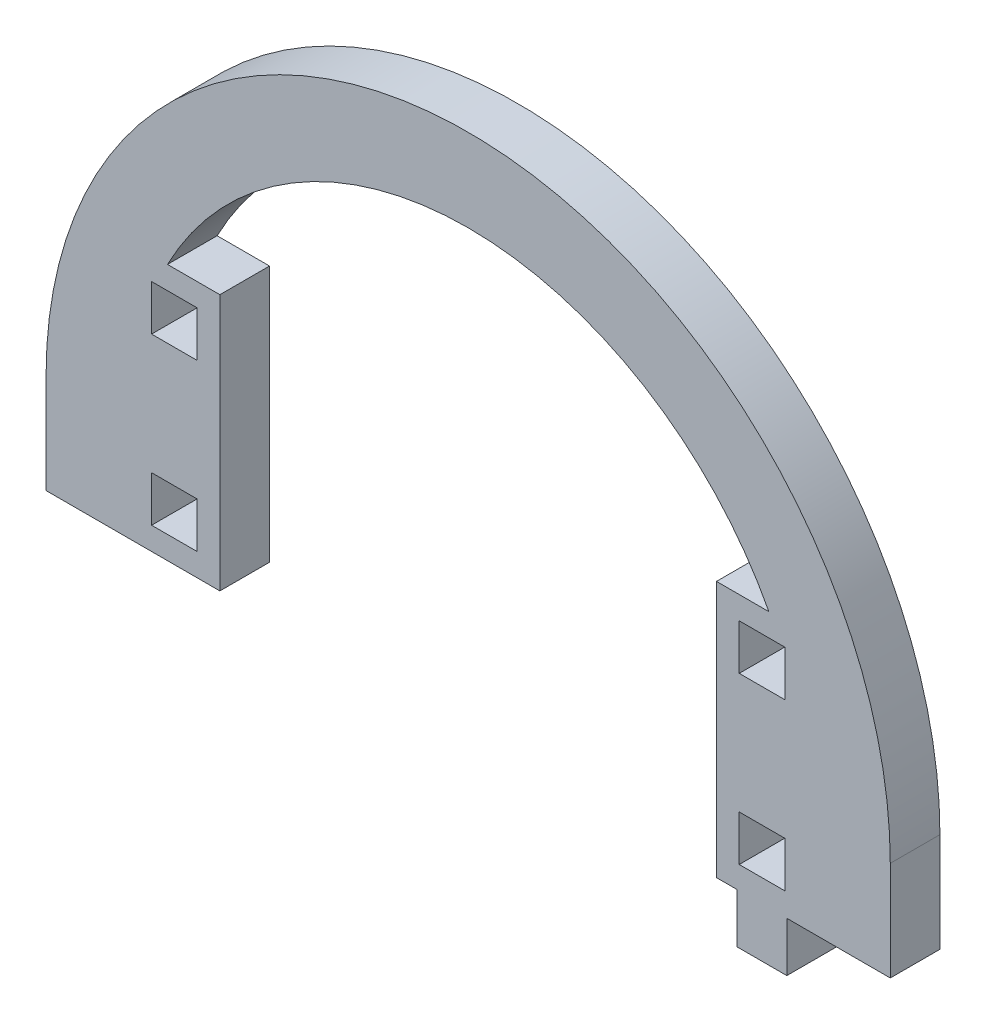
SolidWorks part; units mm, degrees
ref_plane "Front Plane" through (0, 0, 0) normal (0, 0, 1) x (1, 0, 0)
ref_plane "Top Plane" through (0, 0, 0) normal (0, 1, 0) x (1, 0, 0)
ref_plane "Right Plane" through (0, 0, 0) normal (1, 0, 0) x (0, 0, -1)
sketch "Model" plane through (0, 0, 0) normal (0, 0, 1) x (1, 0, 0)
  line L0 (3012.6171, 1236.9472) -> (3012.6171, 1224.9472)
  line L1 (3114.6171, 1236.9472) -> (3114.6171, 1224.9472)
  line L2 (3022.6171, 1224.9472) -> (3012.6171, 1224.9472)
  line L3 (3101.8671, 1233.1972) -> (3096.3671, 1233.1972)
  line L4 (3096.3671, 1233.1972) -> (3096.3671, 1227.6972)
  line L5 (3096.3671, 1227.6972) -> (3101.8671, 1227.6972)
  line L6 (3101.8671, 1227.6972) -> (3101.8671, 1233.1972)
  line L7 (3093.6171, 1224.9472) -> (3096.1171, 1224.9472)
  line L8 (3096.1171, 1224.9472) -> (3096.1171, 1218.9472)
  line L9 (3096.1171, 1218.9472) -> (3102.1171, 1218.9472)
  line L10 (3102.1171, 1218.9472) -> (3102.1171, 1224.9472)
  line L11 (3101.8671, 1253.1972) -> (3096.3671, 1253.1972)
  line L12 (3096.3671, 1253.1972) -> (3096.3671, 1247.6972)
  line L13 (3096.3671, 1247.6972) -> (3101.8671, 1247.6972)
  line L14 (3101.8671, 1247.6972) -> (3101.8671, 1253.1972)
  line L15 (3099.9489, 1255.9472) -> (3093.6171, 1255.9472)
  line L16 (3030.8671, 1233.1972) -> (3025.3671, 1233.1972)
  line L17 (3025.3671, 1233.1972) -> (3025.3671, 1227.6972)
  line L18 (3025.3671, 1227.6972) -> (3030.8671, 1227.6972)
  line L19 (3030.8671, 1227.6972) -> (3030.8671, 1233.1972)
  line L20 (3022.6171, 1224.9472) -> (3033.6171, 1224.9472)
  line L21 (3030.8671, 1253.1972) -> (3025.3671, 1253.1972)
  line L22 (3025.3671, 1253.1972) -> (3025.3671, 1247.6972)
  line L23 (3025.3671, 1247.6972) -> (3030.8671, 1247.6972)
  line L24 (3030.8671, 1247.6972) -> (3030.8671, 1253.1972)
  line L25 (3033.6171, 1255.9472) -> (3027.2853, 1255.9472)
  line L26 (3033.6171, 1255.9472) -> (3033.6171, 1224.9472)
  line L27 (3093.6171, 1255.9472) -> (3093.6171, 1224.9472)
  line L28 (3102.1171, 1224.9472) -> (3114.6171, 1224.9472)
  arc A0 (3114.6171, 1236.9472) -> (3012.6171, 1236.9472) centre (3063.6171, 1236.9472) ccw
  arc A1 (3099.9489, 1255.9472) -> (3027.2853, 1255.9472) centre (3063.6171, 1236.9472) ccw
extrude "Boss-Extrude1" add sketch "Model" along normal blind 6 contours L23 L24 L21 L22 | L18 L19 L16 L17 | L13 L14 L11 L12 | L5 L6 L3 L4 | L0 L2 L20 L26 L25 A1 L15 L27 L7 L8 L9 L10 L28 L1 A0
